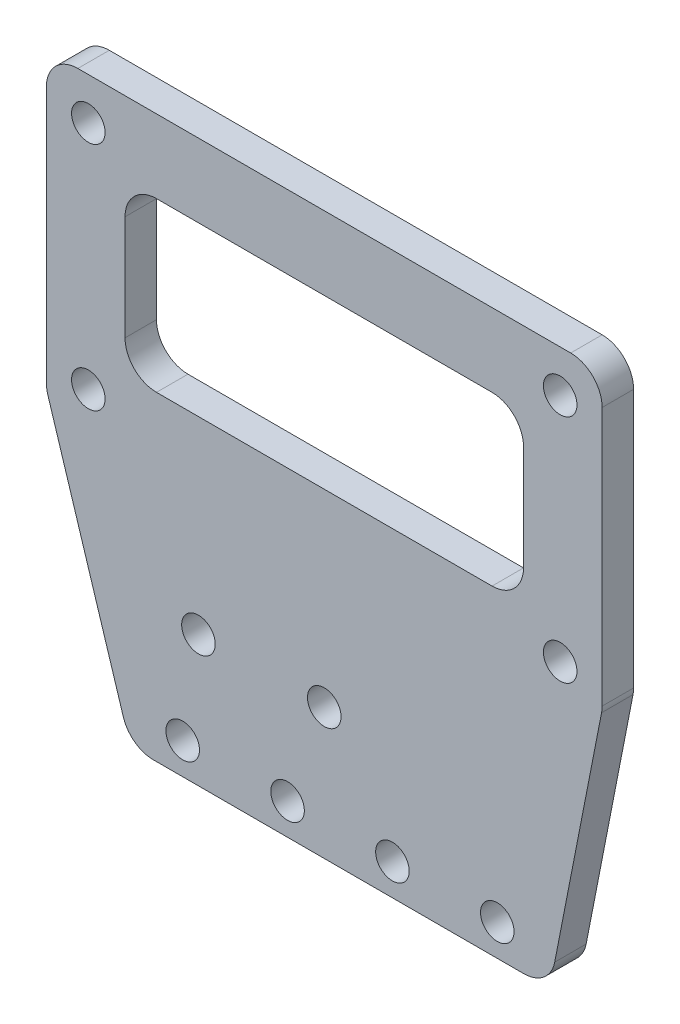
SolidWorks part; units mm, degrees
material "Hexcel AS4C (3000 丝)"
ref_plane "前视基准面" through (0, 0, 0) normal (0, 0, 1) x (1, 0, 0)
ref_plane "上视基准面" through (0, 0, 0) normal (0, 1, 0) x (1, 0, 0)
ref_plane "右视基准面" through (0, 0, 0) normal (1, 0, 0) x (0, 0, -1)
sketch "草图1" plane through (0, 0, 0) normal (0, 0, 1) x (1, 0, 0)
  line L0 (-40, 0) -> (-48, 25.5444)
  line L1 (0, 0) -> (-40, 0)
  line L5 (1, 49.5) -> (-44, 49.5) construction
  line L6 (1, 49.5) -> (1, 27.5) construction
  line L7 (1, 27.5) -> (-44, 27.5) construction
  line L8 (-44, 49.5) -> (-44, 27.5) construction
  line L9 (1, 49.5) -> (-44, 27.5) construction
  line L10 (1, 27.5) -> (-44, 49.5) construction
  line L11 (-48, 25.5444) -> (-48, 53.5)
  line L13 (7, -1.4222) -> (7, 51.7153) construction
  line L16 (-48, 53.5) -> (5, 53.5)
  line L17 (5, 53.5) -> (5, 25.5444)
  line L18 (5, 25.5444) -> (0, 0)
  circle A0 centre (-44, 49.5) radius 1.6
  circle A1 centre (1, 49.5) radius 1.6
  circle A2 centre (1, 27.5) radius 1.6
  circle A3 centre (-44, 27.5) radius 1.6
  point P5 (-21.5, 38.5)
  point P18 (-44, 38.5)
  dimension "D5" = 3.2
  dimension "D1" = 27.5
  dimension "D2" = 40
  dimension "D3" = 22
  dimension "D4" = 45
  dimension "D6" = 7
  dimension "D7" = 4
  dimension "D8" = 6
  dimension "D9" = 4
  dimension "D10" = 4
extrude "凸台-拉伸1" add sketch "草图1" along normal blind 3
sketch "草图2" plane through (0, 0, 3) normal (0, 0, 1) x (1, 0, 0)
  line L1 (-5, 3) -> (-15, 3) construction
  line L2 (-40, 0) -> (0, 0) construction
  circle A0 centre (-5, 3) radius 1.6
  circle A1 centre (-15, 3) radius 1.6
  circle A2 centre (-25, 3) radius 1.6
  circle A3 centre (-35, 3) radius 1.6
  dimension "D1" = 5
  dimension "D2" = 3.2
  dimension "D3" = 3
  dimension "D5" = 10
  dimension "D4" = 4
extrude "切除-拉伸1" cut sketch "草图2" against normal through all
fillet "圆角1" radius 3 6 edges at (-48, 25.5444, 1.5) (-40, 0, 1.5) (0, 0, 1.5) (5, 25.5444, 1.5) (5, 53.5, 1.5) (-48, 53.5, 1.5)
sketch "草图4" plane through (0, 0, 3) normal (0, 0, 1) x (1, 0, 0)
  line L0 (-44, 49.5) -> (1, 49.5) construction
  line L1 (-21.5, 36.5) -> (-21.5, 12.5) construction
  line L2 (-21.5, 12.5) -> (-33.5, 12.5) construction
  line L3 (-33.5, 12.5) -> (-21.5, 36.5) construction
  line L4 (5, 25.8353) -> (0, 17.175) construction
  line L5 (28.5, 54.5) -> (-7.5, 54.5) construction
  line L6 (28.5, 54.5) -> (28.5, 18.5) construction
  line L7 (28.5, 18.5) -> (-7.5, 18.5) construction
  line L8 (-7.5, 54.5) -> (-7.5, 18.5) construction
  line L9 (28.5, 54.5) -> (-7.5, 18.5) construction
  line L10 (28.5, 18.5) -> (-7.5, 54.5) construction
  line L11 (0, 17.175) -> (0, 8.0342) construction
  line L12 (0, 8.0342) -> (1.1744, 6) construction
  line L13 (0.4744, 2.4237) -> (4.9441, 25.259) construction
  line L14 (1.1744, 6) -> (5, 6) construction
  line L15 (5, 6) -> (5, 25.8353) construction
  line L16 (5, 25.8353) -> (5, 50.5) construction
  line L17 (-37.7959, 0) -> (-2.4697, 0) construction
  circle A0 centre (-44, 27.5) radius 1.6 construction
  circle A1 centre (-21.5, 36.5) radius 1.6
  circle A2 centre (-33.5, 12.5) radius 1.6
  circle A3 centre (-21.5, 12.5) radius 1.6
  circle A4 centre (-7.5, 18.5) radius 1.35 construction
  circle A5 centre (-7.5, 54.5) radius 1.35 construction
  circle A6 centre (28.5, 54.5) radius 1.35 construction
  circle A7 centre (28.5, 18.5) radius 1.35 construction
  circle A8 centre (-7.5, 18.5) radius 3 construction
  point P6 (10.5, 36.5)
  point P13 (-21.5, 49.5)
  dimension "D2" = 9
  dimension "D7" = 2.7
  dimension "D8" = 3.2
  dimension "D9" = 6
  dimension "D1" = 24
  dimension "D3" = 12
  dimension "D4" = 32
  dimension "D5" = 36
  dimension "D6" = 36
  dimension "D10" = 5
  dimension "D11" = 30
  dimension "D12" = 30
  dimension "D13" = 6
extrude "切除-拉伸2" cut sketch "草图4" against normal through all
sketch "草图5" plane through (0, 0, 0) normal (0, 0, -1) x (-1, 0, 0)
  line L2 (-1, 49.5) -> (44, 49.5) construction
  line L3 (-1, 49.5) -> (-1, 27.5) construction
  line L4 (-1, 27.5) -> (44, 27.5) construction
  line L5 (44, 49.5) -> (44, 27.5) construction
  line L6 (21.5, 27.5) -> (21.5, 49.5) construction
  line L7 (-1, 38.5) -> (44, 38.5) construction
  line L8 (2.5, 46.5) -> (40.5, 46.5)
  line L9 (2.5, 46.5) -> (2.5, 30.5)
  line L10 (2.5, 30.5) -> (40.5, 30.5)
  line L11 (40.5, 46.5) -> (40.5, 30.5)
  line L12 (21.5, 30.5) -> (21.5, 46.5) construction
  line L13 (2.5, 38.5) -> (40.5, 38.5) construction
  point P5 (21.5, 38.5)
  point P357 (21.5, 38.5)
  dimension "D1" = 3
  dimension "D2" = 3.5
extrude "切除-拉伸3" cut sketch "草图5" against normal through all
fillet "圆角2" radius 3 4 edges at (-40.5, 30.5, 1.5) (-40.5, 46.5, 1.5) (-2.5, 46.5, 1.5) (-2.5, 30.5, 1.5)
